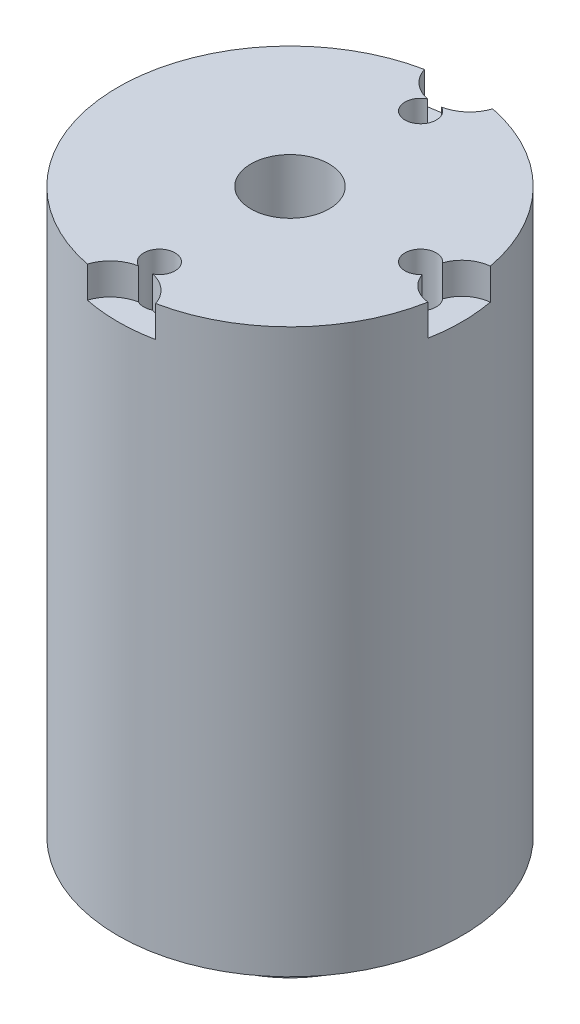
SolidWorks part; units mm, degrees
material "1023 Tôle d'acier au carbone (SS)"
ref_plane "Face" through (0, 0, 0) normal (0, 0, 1) x (1, 0, 0)
ref_plane "Dessus" through (0, 0, 0) normal (0, 1, 0) x (1, 0, 0)
ref_plane "Droite" through (0, 0, 0) normal (1, 0, 0) x (0, 0, -1)
sketch "Esquisse1" plane through (0, 0, 0) normal (0, 1, 0) x (1, 0, 0)
  line L0 (0, 16) -> (0, -18) construction
  circle A2 centre (0, 0) radius 5.5
  dimension "D3" = 11
extrude "Base-Extrusion" add sketch "Esquisse1" against normal blind 18
sketch "Esquisse2" plane through (0, -18, 0) normal (0, -1, 0) x (1, 0, 0)
  circle A0 centre (0, 0) radius 3
  dimension "D1" = 6
extrude "Boss.-Extru.1" add sketch "Esquisse2" along normal blind 1.8
shell "Coque1" thickness 5
sketch "Esquisse3" plane through (0, -19.8, 0) normal (0, -1, 0) x (1, 0, 0)
  circle A0 centre (0, 0) radius 1.25
  dimension "D1" = 2.5
extrude "Enlèv. mat.-Extru.1" cut sketch "Esquisse3" against normal through all
sketch "Esquisse4" plane through (0, 0, 0) normal (0, -1, 0) x (1, 0, 0)
  line L0 (5.5, 0) -> (0, 0) construction
  circle A0 centre (5.5, 0) radius 1
  circle A1 centre (0, -5.75) radius 1.15
  circle A2 centre (0, 5.75) radius 1.15
  circle A3 centre (0, 0) radius 1.25 construction
  dimension "D1" = 11.5
  dimension "D2" = 2.3
  dimension "D3" = 2
  dimension "D4" = 5.5
extrude "Enlèv. mat.-Extru.2" cut sketch "Esquisse4" along normal blind 1
ref_plane "Plan2" through (0, -13.45, 0) normal (0, 1, 0) x (-1, 0, 0)
sketch "Esquisse5" plane through (0, -18, 0) normal (0, -1, 0) x (1, 0, 0)
  circle A0 centre (0, 4.1768) radius 0.5
  dimension "D1" = 1
extrude "Enlèv. mat.-Extru.3" cut sketch "Esquisse5" against normal up to next (18 mm away)
pattern_circular "Répétition circulaire1" count 3 over 180 about axis through (0, 0, 0) along (0, 1, 0) of "Enlèv. mat.-Extru.3"
